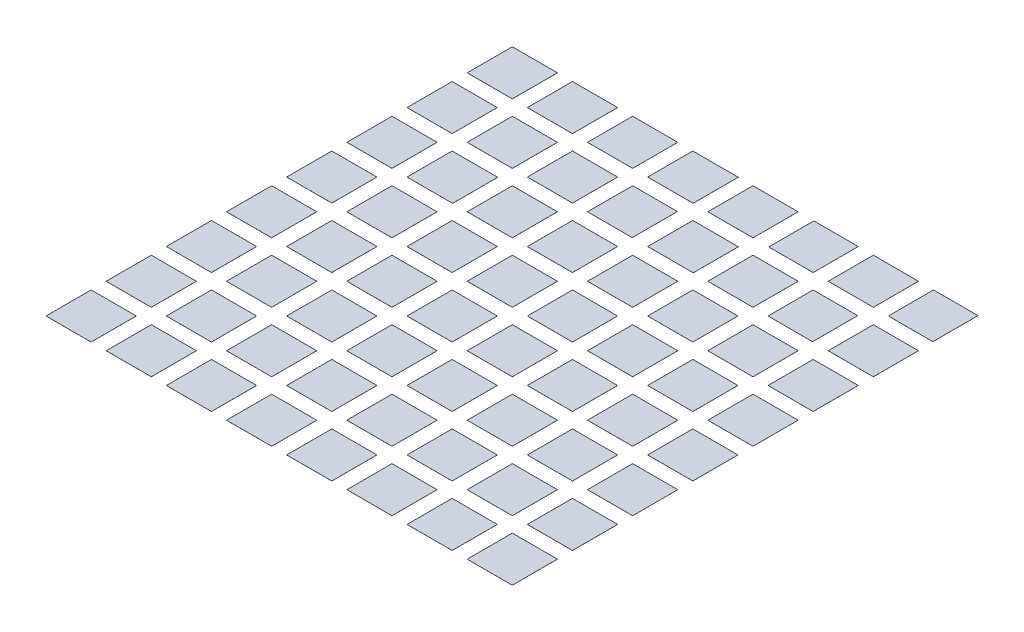
SolidWorks part; units mm, degrees
ref_plane "Front Plane" through (0, 0, 0) normal (0, 0, 1) x (1, 0, 0)
ref_plane "Top Plane" through (0, 0, 0) normal (0, 1, 0) x (1, 0, 0)
ref_plane "Right Plane" through (0, 0, 0) normal (1, 0, 0) x (0, 0, -1)
sketch3d "3DSketch1"
  line L0 (-26.0563, 0, -0.5038) -> (-26.0563, 0, 0.9962)
  line L1 (-26.0563, 0, -0.5038) -> (-24.5563, 0, -0.5038)
  line L2 (-24.5563, 0, -0.5038) -> (-24.5563, 0, 0.9962)
  line L3 (-26.0563, 0, 0.9962) -> (-24.5563, 0, 0.9962)
  line L4 (-24.0563, 0, -0.5038) -> (-24.0563, 0, 0.9962)
  line L5 (-24.0563, 0, -0.5038) -> (-22.5563, 0, -0.5038)
  line L6 (-22.5563, 0, -0.5038) -> (-22.5563, 0, 0.9962)
  line L7 (-24.0563, 0, 0.9962) -> (-22.5563, 0, 0.9962)
  line L8 (-22.0563, 0, -0.5038) -> (-22.0563, 0, 0.9962)
  line L9 (-22.0563, 0, -0.5038) -> (-20.5563, 0, -0.5038)
  line L10 (-20.5563, 0, -0.5038) -> (-20.5563, 0, 0.9962)
  line L11 (-22.0563, 0, 0.9962) -> (-20.5563, 0, 0.9962)
  line L12 (-20.0563, 0, -0.5038) -> (-20.0563, 0, 0.9962)
  line L13 (-20.0563, 0, -0.5038) -> (-18.5453, 0, -0.5038)
  line L14 (-18.5453, 0, -0.5038) -> (-18.5453, 0, 0.9962)
  line L15 (-20.0563, 0, 0.9962) -> (-18.5453, 0, 0.9962)
  line L16 (-18.0563, 0, -0.5038) -> (-18.0563, 0, 0.9962)
  line L17 (-18.0563, 0, -0.5038) -> (-16.5563, 0, -0.5038)
  line L18 (-16.5563, 0, -0.5038) -> (-16.5563, 0, 0.9962)
  line L19 (-18.0563, 0, 0.9962) -> (-16.5563, 0, 0.9962)
  line L20 (-16.0315, 0, -0.5038) -> (-16.0315, 0, 0.9962)
  line L21 (-16.0315, 0, -0.5038) -> (-14.5563, 0, -0.5038)
  line L22 (-14.5563, 0, -0.5038) -> (-14.5563, 0, 0.9962)
  line L23 (-16.0315, 0, 0.9962) -> (-14.5563, 0, 0.9962)
  line L24 (-14.0563, 0, -0.5038) -> (-14.0563, 0, 0.9962)
  line L25 (-14.0563, 0, -0.5038) -> (-12.5563, 0, -0.5038)
  line L26 (-12.5563, 0, -0.5038) -> (-12.5563, 0, 0.9962)
  line L27 (-14.0563, 0, 0.9962) -> (-12.5563, 0, 0.9962)
  line L28 (-12.0563, 0, -0.5038) -> (-12.0563, 0, 0.9962)
  line L29 (-12.0563, 0, -0.5038) -> (-10.5768, 0, -0.5038)
  line L30 (-10.5768, 0, -0.5038) -> (-10.5768, 0, 0.9962)
  line L31 (-12.0563, 0, 0.9962) -> (-10.5768, 0, 0.9962)
  line L32 (-26.0563, 0, 1.4962) -> (-26.0563, 0, 2.9962)
  line L33 (-26.0563, 0, 1.4962) -> (-24.5563, 0, 1.4962)
  line L34 (-24.5563, 0, 1.4962) -> (-24.5563, 0, 2.9962)
  line L35 (-26.0563, 0, 2.9962) -> (-24.5563, 0, 2.9962)
  line L36 (-24.0563, 0, 1.4962) -> (-24.0563, 0, 2.9962)
  line L37 (-24.0563, 0, 1.4962) -> (-22.5563, 0, 1.4962)
  line L38 (-22.5563, 0, 1.4962) -> (-22.5563, 0, 2.9962)
  line L39 (-24.0563, 0, 2.9962) -> (-22.5563, 0, 2.9962)
  line L40 (-22.0563, 0, 1.4962) -> (-22.0563, 0, 2.9962)
  line L41 (-22.0563, 0, 1.4962) -> (-20.5563, 0, 1.4962)
  line L42 (-20.5563, 0, 1.4962) -> (-20.5563, 0, 2.9962)
  line L43 (-22.0563, 0, 2.9962) -> (-20.5563, 0, 2.9962)
  line L44 (-18.0563, 0, 1.4962) -> (-18.0563, 0, 2.9962)
  line L45 (-18.0563, 0, 1.4962) -> (-16.5418, 0, 1.4962)
  line L46 (-16.5418, 0, 1.4962) -> (-16.5418, 0, 2.9962)
  line L47 (-18.0563, 0, 2.9962) -> (-16.5418, 0, 2.9962)
  line L48 (-16.0563, 0, 1.4962) -> (-16.0563, 0, 2.9962)
  line L49 (-16.0563, 0, 1.4962) -> (-14.5563, 0, 1.4962)
  line L50 (-14.5563, 0, 1.4962) -> (-14.5563, 0, 2.9962)
  line L51 (-16.0563, 0, 2.9962) -> (-14.5563, 0, 2.9962)
  line L52 (-14.0563, 0, 1.4962) -> (-14.0563, 0, 2.9962)
  line L53 (-14.0563, 0, 1.4962) -> (-12.5761, 0, 1.4962)
  line L54 (-12.5761, 0, 1.4962) -> (-12.5761, 0, 2.9962)
  line L55 (-14.0563, 0, 2.9962) -> (-12.5761, 0, 2.9962)
  line L56 (-12.0563, 0, 1.4962) -> (-12.0563, 0, 2.9962)
  line L57 (-12.0563, 0, 1.4962) -> (-10.5563, 0, 1.4962)
  line L58 (-10.5563, 0, 1.4962) -> (-10.5563, 0, 2.9962)
  line L59 (-12.0563, 0, 2.9962) -> (-10.5563, 0, 2.9962)
  line L60 (-26.0563, 0, 3.4962) -> (-26.0563, 0, 4.9962)
  line L61 (-26.0563, 0, 3.4962) -> (-24.5563, 0, 3.4962)
  line L62 (-24.5563, 0, 3.4962) -> (-24.5563, 0, 4.9962)
  line L63 (-26.0563, 0, 4.9962) -> (-24.5563, 0, 4.9962)
  line L64 (-24.0563, 0, 3.4962) -> (-24.0563, 0, 4.9962)
  line L65 (-24.0563, 0, 3.4962) -> (-22.5409, 0, 3.4962)
  line L66 (-22.5409, 0, 3.4962) -> (-22.5409, 0, 4.9962)
  line L67 (-24.0563, 0, 4.9962) -> (-22.5409, 0, 4.9962)
  line L68 (-22.0563, 0, 3.4962) -> (-22.0563, 0, 4.9962)
  line L69 (-22.0563, 0, 3.4962) -> (-20.5563, 0, 3.4962)
  line L70 (-20.5563, 0, 3.4962) -> (-20.5563, 0, 4.9962)
  line L71 (-22.0563, 0, 4.9962) -> (-20.5563, 0, 4.9962)
  line L72 (-20.0563, 0, 3.4962) -> (-20.0563, 0, 4.9962)
  line L73 (-20.0563, 0, 3.4962) -> (-18.5563, 0, 3.4962)
  line L74 (-18.5563, 0, 3.4962) -> (-18.5563, 0, 4.9962)
  line L75 (-20.0563, 0, 4.9962) -> (-18.5563, 0, 4.9962)
  line L76 (-18.0563, 0, 3.4962) -> (-18.0563, 0, 4.9962)
  line L77 (-18.0563, 0, 3.4962) -> (-16.5563, 0, 3.4962)
  line L78 (-16.5563, 0, 3.4962) -> (-16.5563, 0, 4.9962)
  line L79 (-18.0563, 0, 4.9962) -> (-16.5563, 0, 4.9962)
  line L80 (-16.0563, 0, 3.4962) -> (-16.0563, 0, 4.9962)
  line L81 (-16.0563, 0, 3.4962) -> (-14.5563, 0, 3.4962)
  line L82 (-14.5563, 0, 3.4962) -> (-14.5563, 0, 4.9962)
  line L83 (-16.0563, 0, 4.9962) -> (-14.5563, 0, 4.9962)
  line L84 (-14.0563, 0, 3.4962) -> (-14.0563, 0, 4.9962)
  line L85 (-14.0563, 0, 3.4962) -> (-12.5563, 0, 3.4962)
  line L86 (-12.5563, 0, 3.4962) -> (-12.5563, 0, 4.9962)
  line L87 (-14.0563, 0, 4.9962) -> (-12.5563, 0, 4.9962)
  line L88 (-12.0563, 0, 3.4962) -> (-12.0563, 0, 4.9962)
  line L89 (-12.0563, 0, 3.4962) -> (-10.5563, 0, 3.4962)
  line L90 (-10.5563, 0, 3.4962) -> (-10.5563, 0, 4.9962)
  line L91 (-12.0563, 0, 4.9962) -> (-10.5563, 0, 4.9962)
  line L92 (-26.0563, 0, 5.4962) -> (-26.0563, 0, 6.9962)
  line L93 (-26.0563, 0, 5.4962) -> (-24.5563, 0, 5.4962)
  line L94 (-24.5563, 0, 5.4962) -> (-24.5563, 0, 6.9962)
  line L95 (-26.0563, 0, 6.9962) -> (-24.5563, 0, 6.9962)
  line L96 (-24.0563, 0, 5.4962) -> (-24.0563, 0, 6.9962)
  line L97 (-24.0563, 0, 5.4962) -> (-22.5563, 0, 5.4962)
  line L98 (-22.5563, 0, 5.4962) -> (-22.5563, 0, 6.9962)
  line L99 (-24.0563, 0, 6.9962) -> (-22.5563, 0, 6.9962)
  line L100 (-22.0563, 0, 5.4962) -> (-22.0563, 0, 6.9962)
  line L101 (-22.0563, 0, 5.4962) -> (-20.5563, 0, 5.4962)
  line L102 (-20.5563, 0, 5.4962) -> (-20.5563, 0, 6.9962)
  line L103 (-22.0563, 0, 6.9962) -> (-20.5563, 0, 6.9962)
  line L104 (-20.0563, 0, 5.4962) -> (-20.0563, 0, 6.9962)
  line L105 (-20.0563, 0, 5.4962) -> (-18.5563, 0, 5.4962)
  line L106 (-18.5563, 0, 5.4962) -> (-18.5563, 0, 6.9962)
  line L107 (-20.0563, 0, 6.9962) -> (-18.5563, 0, 6.9962)
  line L108 (-18.0563, 0, 5.4962) -> (-18.0563, 0, 6.9962)
  line L109 (-18.0563, 0, 5.4962) -> (-16.5563, 0, 5.4962)
  line L110 (-16.5563, 0, 5.4962) -> (-16.5563, 0, 6.9962)
  line L111 (-18.0563, 0, 6.9962) -> (-16.5563, 0, 6.9962)
  line L112 (-16.0563, 0, 5.4962) -> (-16.0563, 0, 6.9962)
  line L113 (-16.0563, 0, 5.4962) -> (-14.5563, 0, 5.4962)
  line L114 (-14.5563, 0, 5.4962) -> (-14.5563, 0, 6.9962)
  line L115 (-16.0563, 0, 6.9962) -> (-14.5563, 0, 6.9962)
  line L116 (-14.0563, 0, 5.4962) -> (-14.0563, 0, 6.9962)
  line L117 (-14.0563, 0, 5.4962) -> (-12.5563, 0, 5.4962)
  line L118 (-12.5563, 0, 5.4962) -> (-12.5563, 0, 6.9962)
  line L119 (-14.0563, 0, 6.9962) -> (-12.5563, 0, 6.9962)
  line L120 (-12.0563, 0, 5.4962) -> (-12.0563, 0, 6.9962)
  line L121 (-12.0563, 0, 5.4962) -> (-10.5563, 0, 5.4962)
  line L122 (-10.5563, 0, 5.4962) -> (-10.5563, 0, 6.9962)
  line L123 (-12.0563, 0, 6.9962) -> (-10.5563, 0, 6.9962)
  line L124 (-26.0563, 0, 7.4962) -> (-26.0563, 0, 8.9962)
  line L125 (-26.0563, 0, 7.4962) -> (-24.5563, 0, 7.4962)
  line L126 (-24.5563, 0, 7.4962) -> (-24.5563, 0, 8.9962)
  line L127 (-26.0563, 0, 8.9962) -> (-24.5563, 0, 8.9962)
  line L128 (-24.0563, 0, 7.4962) -> (-24.0563, 0, 8.9962)
  line L129 (-24.0563, 0, 7.4962) -> (-22.5563, 0, 7.4962)
  line L130 (-22.5563, 0, 7.4962) -> (-22.5563, 0, 8.9962)
  line L131 (-24.0563, 0, 8.9962) -> (-22.5563, 0, 8.9962)
  line L132 (-22.0563, 0, 7.4962) -> (-22.0563, 0, 8.9962)
  line L133 (-22.0563, 0, 7.4962) -> (-20.5563, 0, 7.4962)
  line L134 (-20.5563, 0, 7.4962) -> (-20.5563, 0, 8.9962)
  line L135 (-22.0563, 0, 8.9962) -> (-20.5563, 0, 8.9962)
  line L136 (-20.0563, 0, 7.4962) -> (-20.0563, 0, 8.9962)
  line L137 (-20.0563, 0, 7.4962) -> (-18.5563, 0, 7.4962)
  line L138 (-18.5563, 0, 7.4962) -> (-18.5563, 0, 8.9962)
  line L139 (-20.0563, 0, 8.9962) -> (-18.5563, 0, 8.9962)
  line L140 (-18.0563, 0, 7.4962) -> (-18.0563, 0, 8.9962)
  line L141 (-18.0563, 0, 7.4962) -> (-16.5563, 0, 7.4962)
  line L142 (-16.5563, 0, 7.4962) -> (-16.5563, 0, 8.9962)
  line L143 (-18.0563, 0, 8.9962) -> (-16.5563, 0, 8.9962)
  line L144 (-16.0563, 0, 7.4962) -> (-16.0563, 0, 8.9962)
  line L145 (-16.0563, 0, 7.4962) -> (-14.5563, 0, 7.4962)
  line L146 (-14.5563, 0, 7.4962) -> (-14.5563, 0, 8.9962)
  line L147 (-16.0563, 0, 8.9962) -> (-14.5563, 0, 8.9962)
  line L148 (-14.0563, 0, 7.4962) -> (-14.0563, 0, 8.9962)
  line L149 (-14.0563, 0, 7.4962) -> (-12.5563, 0, 7.4962)
  line L150 (-12.5563, 0, 7.4962) -> (-12.5563, 0, 8.9962)
  line L151 (-14.0563, 0, 8.9962) -> (-12.5563, 0, 8.9962)
  line L152 (-12.0563, 0, 7.4962) -> (-12.0563, 0, 8.9962)
  line L153 (-12.0563, 0, 7.4962) -> (-10.5563, 0, 7.4962)
  line L154 (-10.5563, 0, 7.4962) -> (-10.5563, 0, 8.9962)
  line L155 (-12.0563, 0, 8.9962) -> (-10.5563, 0, 8.9962)
  line L156 (-26.0563, 0, 9.4962) -> (-26.0563, 0, 10.9962)
  line L157 (-26.0563, 0, 9.4962) -> (-24.5563, 0, 9.4962)
  line L158 (-24.5563, 0, 9.4962) -> (-24.5563, 0, 10.9962)
  line L159 (-26.0563, 0, 10.9962) -> (-24.5563, 0, 10.9962)
  line L160 (-24.0563, 0, 9.4962) -> (-24.0563, 0, 10.9962)
  line L161 (-24.0563, 0, 9.4962) -> (-22.5563, 0, 9.4962)
  line L162 (-22.5563, 0, 9.4962) -> (-22.5563, 0, 10.9962)
  line L163 (-24.0563, 0, 10.9962) -> (-22.5563, 0, 10.9962)
  line L164 (-22.0563, 0, 9.4962) -> (-22.0563, 0, 10.9962)
  line L165 (-22.0563, 0, 9.4962) -> (-20.5563, 0, 9.4962)
  line L166 (-20.5563, 0, 9.4962) -> (-20.5563, 0, 10.9962)
  line L167 (-22.0563, 0, 10.9962) -> (-20.5563, 0, 10.9962)
  line L168 (-20.0563, 0, 9.4962) -> (-20.0563, 0, 10.9962)
  line L169 (-20.0563, 0, 9.4962) -> (-18.5563, 0, 9.4962)
  line L170 (-18.5563, 0, 9.4962) -> (-18.5563, 0, 10.9962)
  line L171 (-20.0563, 0, 10.9962) -> (-18.5563, 0, 10.9962)
  line L172 (-18.0563, 0, 9.4962) -> (-18.0563, 0, 10.9962)
  line L173 (-18.0563, 0, 9.4962) -> (-16.5563, 0, 9.4962)
  line L174 (-16.5563, 0, 9.4962) -> (-16.5563, 0, 10.9962)
  line L175 (-18.0563, 0, 10.9962) -> (-16.5563, 0, 10.9962)
  line L176 (-16.0563, 0, 9.4962) -> (-16.0563, 0, 10.9962)
  line L177 (-16.0563, 0, 9.4962) -> (-14.5563, 0, 9.4962)
  line L178 (-14.5563, 0, 9.4962) -> (-14.5563, 0, 10.9962)
  line L179 (-16.0563, 0, 10.9962) -> (-14.5563, 0, 10.9962)
  line L180 (-14.0563, 0, 9.4962) -> (-14.0563, 0, 10.9962)
  line L181 (-14.0563, 0, 9.4962) -> (-12.5563, 0, 9.4962)
  line L182 (-12.5563, 0, 9.4962) -> (-12.5563, 0, 10.9962)
  line L183 (-14.0563, 0, 10.9962) -> (-12.5563, 0, 10.9962)
  line L184 (-26.0563, 0, 11.4962) -> (-26.0563, 0, 12.9962)
  line L185 (-26.0563, 0, 11.4962) -> (-24.5563, 0, 11.4962)
  line L186 (-24.5563, 0, 11.4962) -> (-24.5563, 0, 12.9962)
  line L187 (-26.0563, 0, 12.9962) -> (-24.5563, 0, 12.9962)
  line L188 (-24.0563, 0, 11.4962) -> (-24.0563, 0, 12.9962)
  line L189 (-24.0563, 0, 11.4962) -> (-22.5563, 0, 11.4962)
  line L190 (-22.5563, 0, 11.4962) -> (-22.5563, 0, 12.9962)
  line L191 (-24.0563, 0, 12.9962) -> (-22.5563, 0, 12.9962)
  line L192 (-22.0563, 0, 11.4962) -> (-22.0563, 0, 12.9962)
  line L193 (-22.0563, 0, 11.4962) -> (-20.5563, 0, 11.4962)
  line L194 (-20.5563, 0, 11.4962) -> (-20.5563, 0, 12.9962)
  line L195 (-22.0563, 0, 12.9962) -> (-20.5563, 0, 12.9962)
  line L196 (-20.0563, 0, 11.4962) -> (-20.0563, 0, 12.9962)
  line L197 (-20.0563, 0, 11.4962) -> (-18.5563, 0, 11.4962)
  line L198 (-18.5563, 0, 11.4962) -> (-18.5563, 0, 12.9962)
  line L199 (-20.0563, 0, 12.9962) -> (-18.5563, 0, 12.9962)
  line L200 (-18.0563, 0, 11.4962) -> (-18.0563, 0, 12.9962)
  line L201 (-18.0563, 0, 11.4962) -> (-16.5563, 0, 11.4962)
  line L202 (-16.5563, 0, 11.4962) -> (-16.5563, 0, 12.9962)
  line L203 (-18.0563, 0, 12.9962) -> (-16.5563, 0, 12.9962)
  line L204 (-16.0563, 0, 11.4962) -> (-16.0563, 0, 12.9962)
  line L205 (-16.0563, 0, 11.4962) -> (-14.5563, 0, 11.4962)
  line L206 (-14.5563, 0, 11.4962) -> (-14.5563, 0, 12.9962)
  line L207 (-16.0563, 0, 12.9962) -> (-14.5563, 0, 12.9962)
  line L208 (-14.0563, 0, 11.4962) -> (-14.0563, 0, 12.9962)
  line L209 (-14.0563, 0, 11.4962) -> (-12.5563, 0, 11.4962)
  line L210 (-12.5563, 0, 11.4962) -> (-12.5563, 0, 12.9962)
  line L211 (-14.0563, 0, 12.9962) -> (-12.5563, 0, 12.9962)
  line L212 (-12.0563, 0, 11.4962) -> (-12.0563, 0, 12.9962)
  line L213 (-12.0563, 0, 11.4962) -> (-10.5563, 0, 11.4962)
  line L214 (-10.5563, 0, 11.4962) -> (-10.5563, 0, 12.9962)
  line L215 (-12.0563, 0, 12.9962) -> (-10.5563, 0, 12.9962)
  line L216 (-26.0563, 0, 13.4962) -> (-26.0563, 0, 14.9962)
  line L217 (-26.0563, 0, 13.4962) -> (-24.5563, 0, 13.4962)
  line L218 (-24.5563, 0, 13.4962) -> (-24.5563, 0, 14.9962)
  line L219 (-26.0563, 0, 14.9962) -> (-24.5563, 0, 14.9962)
  line L220 (-24.0563, 0, 13.4962) -> (-24.0563, 0, 14.9962)
  line L221 (-24.0563, 0, 13.4962) -> (-22.5563, 0, 13.4962)
  line L222 (-22.5563, 0, 13.4962) -> (-22.5563, 0, 14.9962)
  line L223 (-24.0563, 0, 14.9962) -> (-22.5563, 0, 14.9962)
  line L224 (-22.0563, 0, 13.4962) -> (-22.0563, 0, 14.9962)
  line L225 (-22.0563, 0, 13.4962) -> (-20.5563, 0, 13.4962)
  line L226 (-20.5563, 0, 13.4962) -> (-20.5563, 0, 14.9962)
  line L227 (-22.0563, 0, 14.9962) -> (-20.5563, 0, 14.9962)
  line L228 (-18.0563, 0, 13.4962) -> (-18.0563, 0, 14.9962)
  line L229 (-18.0563, 0, 13.4962) -> (-16.5563, 0, 13.4962)
  line L230 (-16.5563, 0, 13.4962) -> (-16.5563, 0, 14.9962)
  line L231 (-18.0563, 0, 14.9962) -> (-16.5563, 0, 14.9962)
  line L232 (-16.0563, 0, 13.4962) -> (-16.0563, 0, 14.9962)
  line L233 (-16.0563, 0, 13.4962) -> (-14.5563, 0, 13.4962)
  line L234 (-14.5563, 0, 13.4962) -> (-14.5563, 0, 14.9962)
  line L235 (-16.0563, 0, 14.9962) -> (-14.5563, 0, 14.9962)
  line L236 (-14.0563, 0, 13.4962) -> (-14.0563, 0, 14.9962)
  line L237 (-14.0563, 0, 13.4962) -> (-12.5563, 0, 13.4962)
  line L238 (-12.5563, 0, 13.4962) -> (-12.5563, 0, 14.9962)
  line L239 (-14.0563, 0, 14.9962) -> (-12.5563, 0, 14.9962)
  line L240 (-20.0563, 0, 1.4962) -> (-20.0563, 0, 2.9962)
  line L241 (-20.0563, 0, 1.4962) -> (-18.5694, 0, 1.4962)
  line L242 (-18.5694, 0, 1.4962) -> (-18.5694, 0, 2.9962)
  line L243 (-20.0563, 0, 2.9962) -> (-18.5694, 0, 2.9962)
  line L244 (-20.0563, 0, 13.4962) -> (-20.0563, 0, 14.9962)
  line L245 (-20.0563, 0, 13.4962) -> (-18.5563, 0, 13.4962)
  line L246 (-18.5563, 0, 13.4962) -> (-18.5563, 0, 14.9962)
  line L247 (-20.0563, 0, 14.9962) -> (-18.5563, 0, 14.9962)
  line L248 (-12.0563, 0, 13.4962) -> (-12.0563, 0, 14.9962)
  line L249 (-12.0563, 0, 13.4962) -> (-10.5563, 0, 13.4962)
  line L250 (-10.5563, 0, 13.4962) -> (-10.5563, 0, 14.9962)
  line L251 (-12.0563, 0, 14.9962) -> (-10.5563, 0, 14.9962)
  line L252 (-12.0563, 0, 9.4962) -> (-12.0563, 0, 10.9962)
  line L253 (-12.0563, 0, 9.4962) -> (-10.5563, 0, 9.4962)
  line L254 (-10.5563, 0, 9.4962) -> (-10.5563, 0, 10.9962)
  line L255 (-12.0563, 0, 10.9962) -> (-10.5563, 0, 10.9962)
  line L256 (-22.0563, 0, 14.9962) -> (-22.0563, -0.9722, 14.9962) construction
extrude "Boss-Extrude1" add sketch "3DSketch1" along direction (0, -1, 0) on the side against the normal blind 0.001
